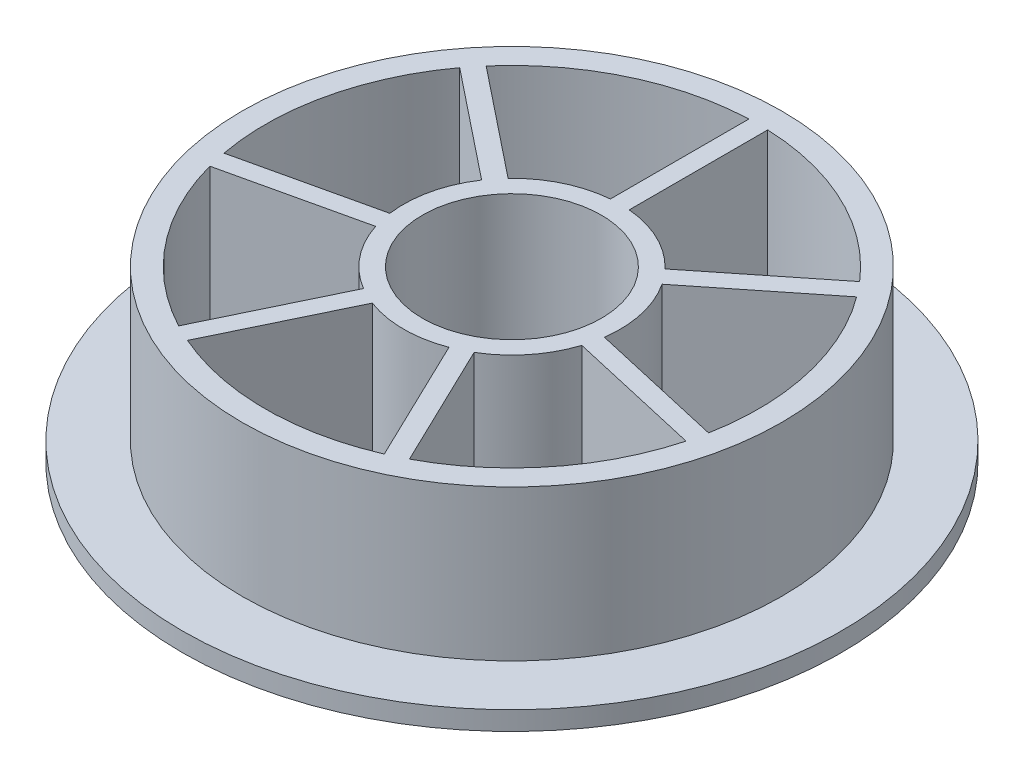
SolidWorks part; units mm, degrees
ref_plane "前视基准面" through (0, 0, 0) normal (0, 0, 1) x (1, 0, 0)
ref_plane "上视基准面" through (0, 0, 0) normal (0, 1, 0) x (1, 0, 0)
ref_plane "右视基准面" through (0, 0, 0) normal (1, 0, 0) x (0, 0, -1)
sketch "草图1" plane through (0, 0, 0) normal (0, 1, 0) x (1, 0, 0)
  line L0 (0, -998.2286) -> (0, 9.5) construction
  line L1 (19.8329, 17.0952) -> (8.3335, 7.9248)
  line L2 (0, 10.4676) -> (0, 50001.7714) construction
  line L3 (-1, 26.1647) -> (-1, 11.4564)
  line L5 (1, 26.1647) -> (1, 11.4564)
  line L7 (21.0798, 15.5316) -> (9.5805, 6.3611)
  line L9 (25.7312, -4.8473) -> (11.3917, -1.5744)
  line L11 (25.2861, -6.7971) -> (10.9467, -3.5242)
  line L13 (12.2534, -23.1397) -> (5.8717, -9.888)
  line L15 (10.4515, -24.0074) -> (4.0698, -10.7558)
  line L17 (-10.4515, -24.0074) -> (-4.0698, -10.7558)
  line L19 (-12.2534, -23.1397) -> (-5.8717, -9.888)
  line L21 (-25.2861, -6.7971) -> (-10.9467, -3.5242)
  line L23 (-25.7312, -4.8473) -> (-11.3917, -1.5744)
  line L25 (-21.0798, 15.5316) -> (-9.5805, 6.3611)
  line L27 (-19.8329, 17.0952) -> (-8.3335, 7.9248)
  circle A0 centre (0, 0) radius 9.5
  arc A1 (-1, 11.4564) -> (-8.3335, 7.9248) centre (0, 0) ccw
  arc A2 (-21.0798, 15.5316) -> (-25.7312, -4.8473) centre (0, 0) ccw
  circle A3 centre (0, 0) radius 35
  arc A4 (-1, 26.1647) -> (-19.8329, 17.0952) centre (0, 0) ccw
  arc A5 (19.8329, 17.0952) -> (1, 26.1647) centre (0, 0) ccw
  arc A6 (25.7312, -4.8473) -> (21.0798, 15.5316) centre (0, 0) ccw
  arc A7 (12.2534, -23.1397) -> (25.2861, -6.7971) centre (0, 0) ccw
  arc A8 (-10.4515, -24.0074) -> (10.4515, -24.0074) centre (0, 0) ccw
  arc A9 (-25.2861, -6.7971) -> (-12.2534, -23.1397) centre (0, 0) ccw
  arc A10 (8.3335, 7.9248) -> (1, 11.4564) centre (0, 0) ccw
  arc A11 (11.3917, -1.5744) -> (9.5805, 6.3611) centre (0, 0) ccw
  arc A12 (5.8717, -9.888) -> (10.9467, -3.5242) centre (0, 0) ccw
  arc A13 (-4.0698, -10.7558) -> (4.0698, -10.7558) centre (0, 0) ccw
  arc A14 (-10.9467, -3.5242) -> (-5.8717, -9.888) centre (0, 0) ccw
  arc A15 (-9.5805, 6.3611) -> (-11.3917, -1.5744) centre (0, 0) ccw
  point P38 (0, 0)
  dimension "D1" = 19
  dimension "D2" = 23
  dimension "D3" = 70
  dimension "D4" = 7
extrude "凸台-拉伸1" add sketch "草图1" along normal blind 18
sketch "草图2" plane through (0, 18, 0) normal (0, 1, 0) x (1, 0, 0)
  circle A0 centre (0, 0) radius 40.8564
  circle A1 centre (0, 0) radius 28.6507
extrude "切除-拉伸1" cut sketch "草图2" against normal blind 16
